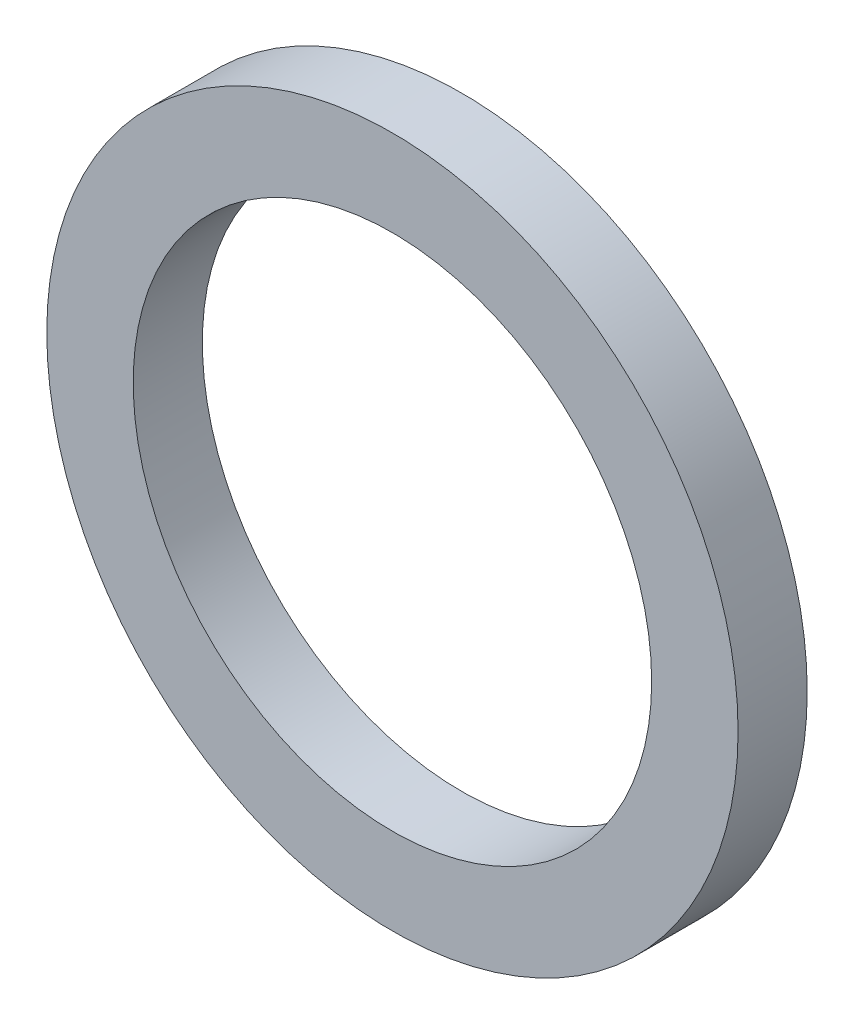
SolidWorks part; units mm, degrees
ref_plane "Plan de face" through (0, 0, 0) normal (0, 0, 1) x (1, 0, 0)
ref_plane "Plan de dessus" through (0, 0, 0) normal (0, 1, 0) x (1, 0, 0)
ref_plane "Plan de droite" through (0, 0, 0) normal (1, 0, 0) x (0, 0, -1)
sketch "Esquisse8" plane through (0, 0, 0) normal (0, 0, 1) x (1, 0, 0)
  circle A0 centre (0, 0) radius 7.5
  circle A1 centre (0, 0) radius 10
extrude "Extrusion3" add sketch "Esquisse8" along normal blind 2
